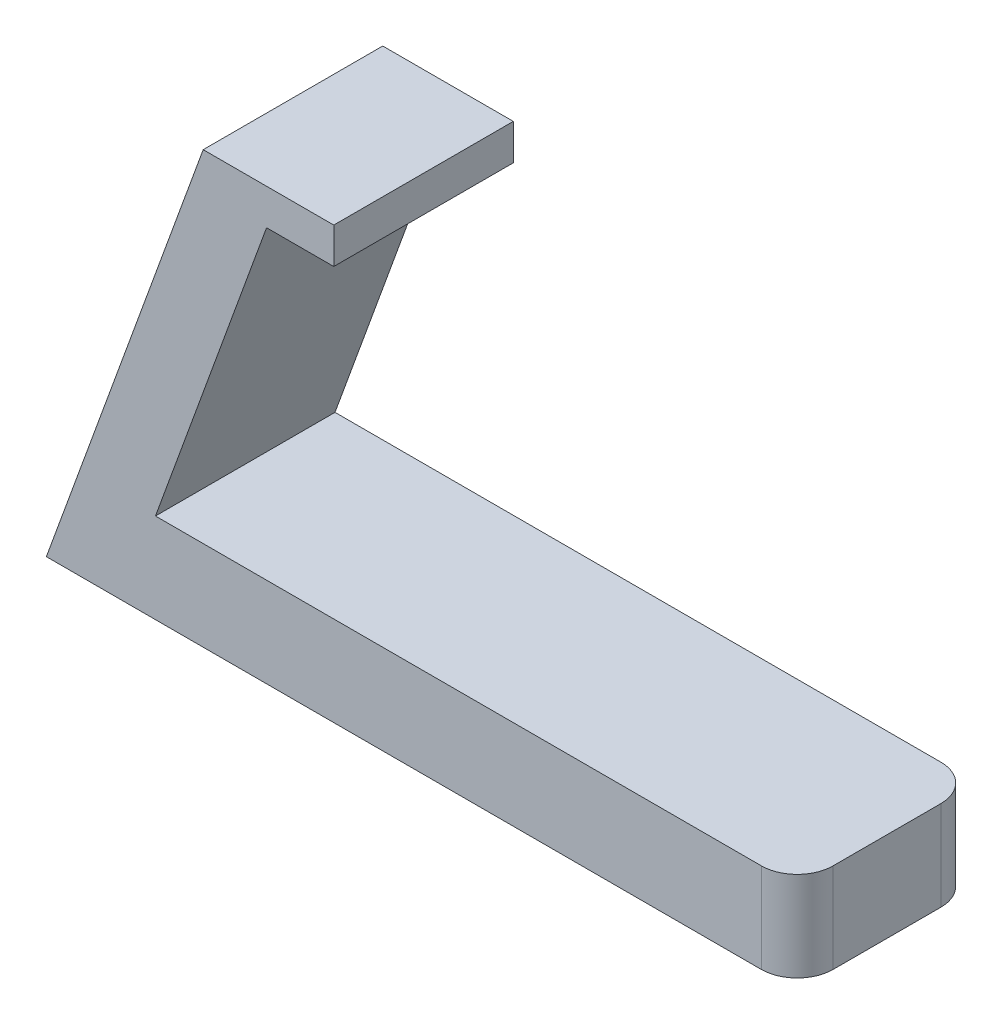
SolidWorks part; units mm, degrees
ref_plane "Front Plane" through (0, 0, 0) normal (0, 0, 1) x (1, 0, 0)
ref_plane "Top Plane" through (0, 0, 0) normal (0, 1, 0) x (1, 0, 0)
ref_plane "Right Plane" through (0, 0, 0) normal (1, 0, 0) x (0, 0, -1)
sketch "Sketch1" plane through (0, 0, 0) normal (0, 1, 0) x (1, 0, 0)
  line L1 (0, 0) -> (50.8, 0)
  line L2 (0, 0) -> (0, 12.7)
  line L3 (0, 12.7) -> (50.8, 12.7)
  line L4 (50.8, 0) -> (50.8, 12.7)
  dimension "D1" = 50.8
  dimension "D2" = 12.7
extrude "Boss-Extrude1" add sketch "Sketch1" along normal blind 6.35
fillet "Fillet1" radius 2.54 2 edges at (50.8, 3.175, 0) (50.8, 3.175, -12.7)
sketch "Sketch3" plane through (0, 0, 0) normal (0, 0, 1) x (1, 0, 0)
  line L0 (-2.3112, 0) -> (7.8581, 27.94)
  line L1 (-2.3112, 0) -> (3.0948, 0)
  line L2 (0, 0) -> (48.26, 0) construction
  line L3 (3.0948, 0) -> (13.2641, 27.94)
  line L4 (13.2641, 27.94) -> (7.8581, 27.94)
  line L5 (0, 6.35) -> (48.26, 6.35) construction
  point P3 (-3.8664, 0)
  point P5 (18.0948, 18.4628)
  point P7 (2.0092, 0)
  dimension "D1" = 5.08
  dimension "D2" = 27.94
  dimension "D3" = 70
extrude "Boss-Extrude2" add sketch "Sketch3" against normal up to surface (12.7 mm away) up to face at (24.13, 3.175, -12.7)
sketch "Sketch4" plane through (0, 0, 0) normal (0, 0, 1) x (1, 0, 0)
  line L4 (7.8581, 27.94) -> (18.0181, 27.94)
  line L5 (18.0181, 27.94) -> (18.0181, 30.48)
  line L6 (18.0181, 30.48) -> (8.7826, 30.48)
  line L7 (8.7826, 30.48) -> (7.8581, 27.94)
  line L8 (7.8581, 27.94) -> (-2.3112, 0) construction
  point P7 (20.0005, 30.426)
  dimension "D1" = 2.54
  dimension "D2" = 10.16
extrude "Boss-Extrude3" add sketch "Sketch4" against normal up to surface (12.7 mm away) up to face at (20.1228, 11.43, -12.7)
